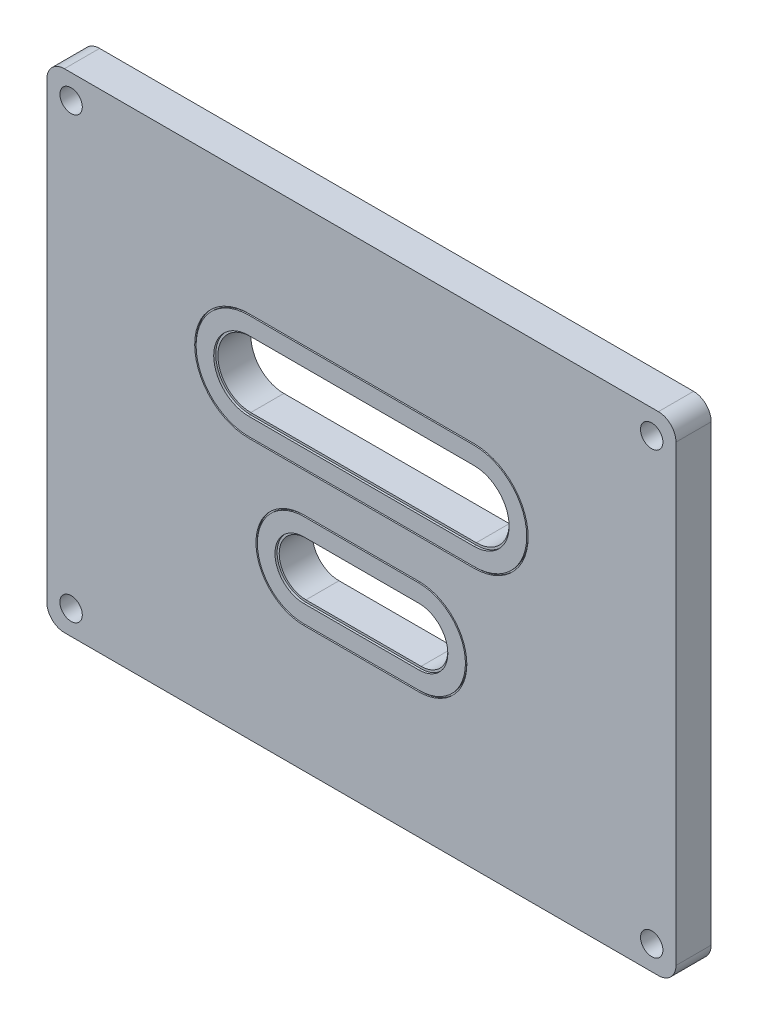
SolidWorks part; units mm, degrees
material "6061 Alloy"
ref_plane "Front Plane" through (0, 0, 0) normal (0, 0, 1) x (1, 0, 0)
ref_plane "Top Plane" through (0, 0, 0) normal (0, 1, 0) x (1, 0, 0)
ref_plane "Right Plane" through (0, 0, 0) normal (1, 0, 0) x (0, 0, -1)
sketch "Sketch1" plane through (0, 0, 0) normal (0, 0, 1) x (1, 0, 0)
  line L0 (-63.5, 0) -> (63.5, 0) construction
  line L1 (0, 50.8) -> (0, -50.8) construction
  line L3 (-56.769, 44.069) -> (56.769, 44.069)
  line L4 (-56.769, 44.069) -> (-56.769, -44.069)
  line L5 (-56.769, -44.069) -> (56.769, -44.069)
  line L6 (56.769, 44.069) -> (56.769, -44.069)
  dimension "D1" = 88.138
  dimension "D2" = 113.538
extrude "Extrude1" add sketch "Sketch1" along normal blind 6.35
sketch "Sketch6" plane through (0, 0, 6.35) normal (0, 0, 1) x (1, 0, 0)
  line L0 (-56.769, 39.6875) -> (56.769, 39.6875) construction
  line L1 (-56.769, 44.069) -> (-56.769, -44.069) construction
  line L2 (56.769, -44.069) -> (56.769, 44.069) construction
  line L3 (-56.769, -39.6875) -> (56.769, -39.6875) construction
  line L4 (52.3875, 44.069) -> (52.3875, -44.069) construction
  line L5 (56.769, 44.069) -> (-56.769, 44.069) construction
  line L6 (-56.769, -44.069) -> (56.769, -44.069) construction
  line L7 (-52.3875, 44.069) -> (-52.3875, -44.069) construction
  line L8 (-56.769, 0) -> (56.769, 0) construction
  line L9 (0, 44.069) -> (0, -44.069) construction
  dimension "D1" = 104.775
  dimension "D2" = 79.375
hole_wizard "#8 Clearance Hole1" positions "3DSketch2" profile "Sketch7" hole size "#8" standard "Ansi Inch" end condition up to next
sketch3d "3DSketch2"
  line L0 (-52.3875, 44.069, 6.35) -> (-52.3875, -44.069, 6.35) construction
  line L1 (52.3875, 44.069, 6.35) -> (52.3875, -44.069, 6.35) construction
  line L2 (-56.769, -39.6875, 6.35) -> (56.769, -39.6875, 6.35) construction
  line L3 (-56.769, 39.6875, 6.35) -> (56.769, 39.6875, 6.35) construction
  point P0 (-52.3875, 39.6875, 6.35)
  point P4 (52.3875, 39.6875, 6.35)
  point P8 (52.3875, -39.6875, 6.35)
  point P12 (-52.3875, -39.6875, 6.35)
sketch "Sketch7" plane through (-52.3875, 39.6875, 6.35) normal (1, 0, 0) x (0, -1, 0)
  line L0 (0, 0) -> (0, 6.35)
  line L1 (0, 6.35) -> (2.0193, 6.35)
  line L2 (2.0193, 6.35) -> (2.0193, 0)
  line L5 (2.0193, 0) -> (0, 0)
  line L11 (0, -6.35) -> (0, 107.95) construction
  dimension "Thru Hole Dia." = 4.0386
  dimension "Thru Hole Depth" = 6.35
fillet "Fillet2" radius 3.175 4 edges at (-56.769, -44.069, 3.175) (56.769, -44.069, 3.175) (56.769, 44.069, 3.175) (-56.769, 44.069, 3.175)
sketch "Sketch8" plane through (0, 0, 6.35) normal (0, 0, 1) x (1, 0, 0)
  line L0 (53.594, 44.069) -> (-53.594, 44.069) construction
  line L1 (20.3454, 19.0119) -> (-20.3454, 19.0119)
  line L2 (20.3454, 19.0119) -> (20.3454, 6.3881)
  line L3 (20.3454, 6.3881) -> (-20.3454, 6.3881)
  line L4 (-20.3454, 19.0119) -> (-20.3454, 6.3881)
  line L5 (20.3454, 19.0119) -> (-20.3454, 6.3881) construction
  line L6 (20.3454, 6.3881) -> (-20.3454, 19.0119) construction
  line L7 (10.3886, -17.907) -> (-10.3886, -17.907)
  line L8 (10.3886, -17.907) -> (10.3886, -7.493)
  line L9 (10.3886, -7.493) -> (-10.3886, -7.493)
  line L10 (-10.3886, -17.907) -> (-10.3886, -7.493)
  line L11 (10.3886, -17.907) -> (-10.3886, -7.493) construction
  line L12 (10.3886, -7.493) -> (-10.3886, -17.907) construction
  arc A0 (-20.3454, 6.3881) -> (-20.3454, 19.0119) centre (-20.3454, 12.7) cw
  arc A1 (20.3454, 19.0119) -> (20.3454, 6.3881) centre (20.3454, 12.7) cw
  arc A2 (10.3886, -7.493) -> (10.3886, -17.907) centre (10.3886, -12.7) cw
  arc A3 (-10.3886, -7.493) -> (-10.3886, -17.907) centre (-10.3886, -12.7) ccw
  point P0 (0, 12.7)
  point P5 (0, -12.7)
  point P18 (-15.5956, -12.7)
  point P19 (15.5956, -12.7)
  point P20 (-26.6573, 12.7)
  point P21 (26.6573, 12.7)
  dimension "D1" = 31.1912
  dimension "D2" = 53.3146
  dimension "D3" = 12.6238
  dimension "D4" = 10.414
  dimension "D5" = 31.369
  dimension "D6" = 56.769
extrude "Cut-Extrude1" cut sketch "Sketch8" against normal blind 0.381 contours A0 L4 | L1 L4 L3 L2 | A1 L2 | A2 L8 | L10 L7 L8 L9 | L10 A3
sketch "Sketch9" plane through (0, 0, 6.35) normal (0, 0, 1) x (1, 0, 0)
  line L12 (-20.3454, 6.7691) -> (20.3454, 6.7691)
  line L13 (20.3454, 18.6309) -> (-20.3454, 18.6309)
  line L14 (-20.3454, 6.7691) -> (20.3454, 6.7691)
  line L15 (20.3454, 18.6309) -> (-20.3454, 18.6309)
  line L18 (10.3886, -7.874) -> (-10.3886, -7.874)
  line L19 (-10.3886, -17.526) -> (10.3886, -17.526)
  line L20 (10.3886, -7.874) -> (-10.3886, -7.874)
  line L21 (-10.3886, -17.526) -> (10.3886, -17.526)
  arc A12 (-20.3454, 18.6309) -> (-20.3454, 6.7691) centre (-20.3454, 12.7) ccw
  arc A13 (20.3454, 6.7691) -> (20.3454, 18.6309) centre (20.3454, 12.7) ccw
  arc A14 (-20.3454, 18.6309) -> (-20.3454, 6.7691) centre (-20.3454, 12.7) ccw
  arc A15 (20.3454, 6.7691) -> (20.3454, 18.6309) centre (20.3454, 12.7) ccw
  arc A18 (10.3886, -17.526) -> (10.3886, -7.874) centre (10.3886, -12.7) ccw
  arc A19 (-10.3886, -7.874) -> (-10.3886, -17.526) centre (-10.3886, -12.7) ccw
  arc A20 (10.3886, -17.526) -> (10.3886, -7.874) centre (10.3886, -12.7) ccw
  arc A21 (-10.3886, -7.874) -> (-10.3886, -17.526) centre (-10.3886, -12.7) ccw
  dimension "D1" = 0.381
  dimension "D2" = 0.381
extrude "Cut-Extrude2" cut sketch "Sketch9" against normal through all
sketch "Sketch10" plane through (0, 0, 6.35) normal (0, 0, 1) x (1, 0, 0)
  line L0 (20.3454, 6.3881) -> (-20.3454, 6.3881) construction
  line L1 (20.3454, 19.0119) -> (-20.3454, 19.0119) construction
  line L2 (20.3454, 6.3881) -> (-20.3454, 6.3881)
  line L3 (20.3454, 19.0119) -> (-20.3454, 19.0119)
  line L4 (20.3454, 3.2131) -> (-20.3454, 3.2131)
  line L5 (20.3454, 22.1869) -> (-20.3454, 22.1869)
  line L6 (10.3886, -7.493) -> (-10.3886, -7.493) construction
  line L7 (10.3886, -17.907) -> (-10.3886, -17.907) construction
  line L8 (10.3886, -7.493) -> (-10.3886, -7.493)
  line L9 (10.3886, -17.907) -> (-10.3886, -17.907)
  line L10 (10.3886, -21.082) -> (-10.3886, -21.082)
  line L11 (10.3886, -4.318) -> (-10.3886, -4.318)
  line L12 (20.3454, 2.9591) -> (-20.3454, 2.9591)
  line L13 (20.3454, 22.4409) -> (-20.3454, 22.4409)
  line L14 (10.3886, -21.336) -> (-10.3886, -21.336)
  line L15 (10.3886, -4.064) -> (-10.3886, -4.064)
  arc A0 (20.3454, 6.3881) -> (20.3454, 19.0119) centre (20.3454, 12.7) ccw construction
  arc A1 (-20.3454, 19.0119) -> (-20.3454, 6.3881) centre (-20.3454, 12.7) ccw construction
  arc A2 (20.3454, 6.3881) -> (20.3454, 19.0119) centre (20.3454, 12.7) ccw
  arc A3 (-20.3454, 19.0119) -> (-20.3454, 6.3881) centre (-20.3454, 12.7) ccw
  arc A4 (-20.3454, 22.1869) -> (-20.3454, 3.2131) centre (-20.3454, 12.7) ccw
  arc A5 (20.3454, 3.2131) -> (20.3454, 22.1869) centre (20.3454, 12.7) ccw
  arc A6 (10.3886, -17.907) -> (10.3886, -7.493) centre (10.3886, -12.7) ccw construction
  arc A7 (-10.3886, -7.493) -> (-10.3886, -17.907) centre (-10.3886, -12.7) ccw construction
  arc A8 (10.3886, -17.907) -> (10.3886, -7.493) centre (10.3886, -12.7) ccw
  arc A9 (-10.3886, -7.493) -> (-10.3886, -17.907) centre (-10.3886, -12.7) ccw
  arc A10 (-10.3886, -4.318) -> (-10.3886, -21.082) centre (-10.3886, -12.7) ccw
  arc A11 (10.3886, -21.082) -> (10.3886, -4.318) centre (10.3886, -12.7) ccw
  arc A12 (-20.3454, 22.4409) -> (-20.3454, 2.9591) centre (-20.3454, 12.7) ccw
  arc A13 (20.3454, 2.9591) -> (20.3454, 22.4409) centre (20.3454, 12.7) ccw
  arc A14 (-10.3886, -4.064) -> (-10.3886, -21.336) centre (-10.3886, -12.7) ccw
  arc A15 (10.3886, -21.336) -> (10.3886, -4.064) centre (10.3886, -12.7) ccw
  dimension "D1" = 3.175
  dimension "D2" = 3.175
  dimension "D3" = 0.254
  dimension "D4" = 0.254
extrude "Cut-Extrude3" cut sketch "Sketch10" against normal blind 0.254 contours L12 A13 L13 A12 A5 L4 A4 L5 | L14 A15 L15 A14 A11 L10 A10 L11
